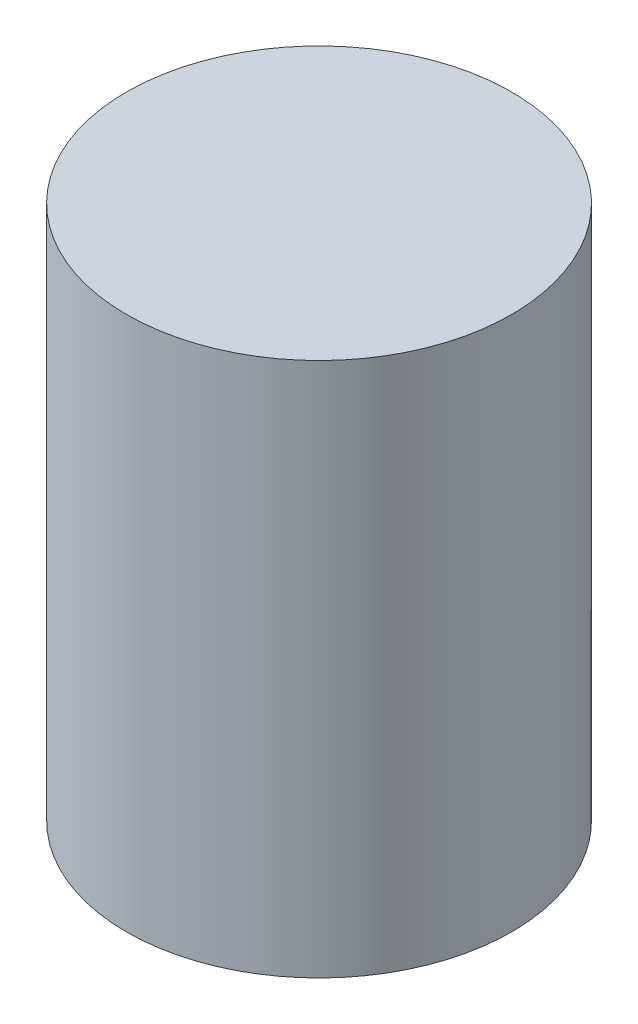
SolidWorks part; units mm, degrees
material "AISI Type 316L stainless steel"
ref_plane "Front Plane" through (0, 0, 0) normal (0, 0, 1) x (1, 0, 0)
ref_plane "Top Plane" through (0, 0, 0) normal (0, 1, 0) x (1, 0, 0)
ref_plane "Right Plane" through (0, 0, 0) normal (1, 0, 0) x (0, 0, -1)
sketch "Sketch1" plane through (0, 0, 0) normal (0, 1, 0) x (1, 0, 0)
  circle A0 centre (0, 0) radius 9.723
  dimension "D1" = 19.446
extrude "Boss-Extrude1" add sketch "Sketch1" along normal mid plane 26.9875
